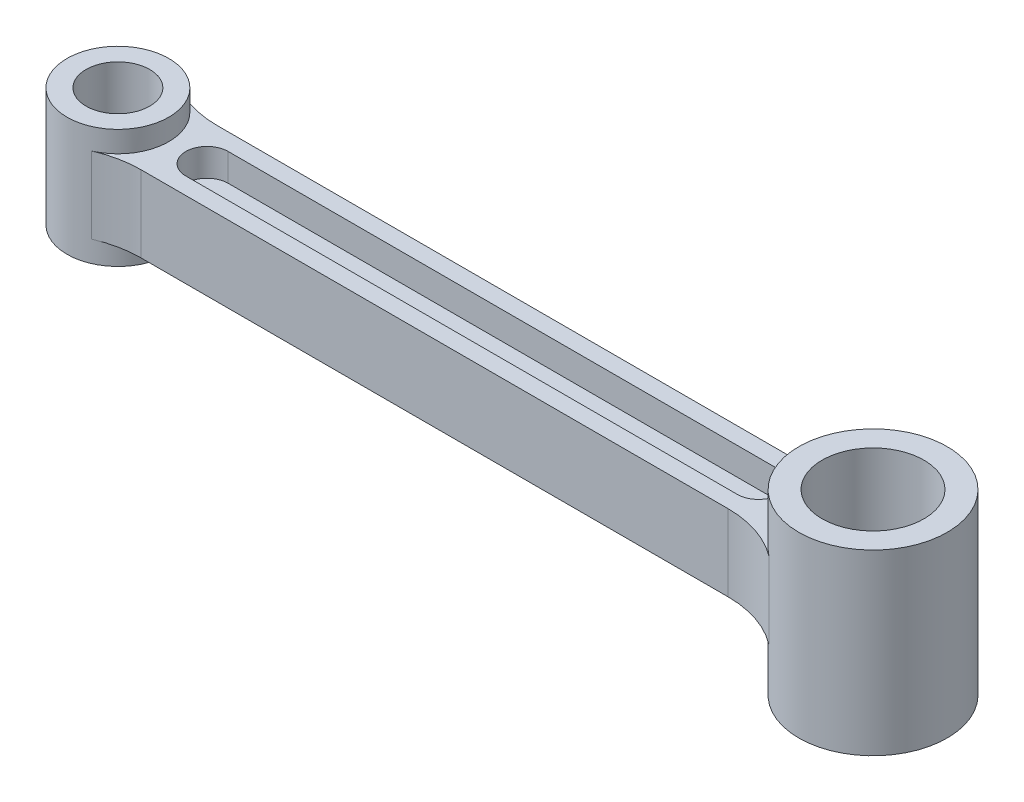
SolidWorks part; units mm, degrees
ref_plane "Front Plane" through (0, 0, 0) normal (0, 0, 1) x (1, 0, 0)
ref_plane "Top Plane" through (0, 0, 0) normal (0, 1, 0) x (1, 0, 0)
ref_plane "Right Plane" through (0, 0, 0) normal (1, 0, 0) x (0, 0, -1)
sketch "Sketch1" plane through (0, 0, 0) normal (0, 1, 0) x (1, 0, 0)
  circle A0 centre (0, 0) radius 7.5
  circle A1 centre (0, 0) radius 12
  dimension "D1" = 24
  dimension "D2" = 15
extrude "Boss-Extrude1" add sketch "Sketch1" along normal mid plane 28
sketch "Sketch3" plane through (0, 0, 0) normal (0, 1, 0) x (1, 0, 0)
  circle A0 centre (178, 0) radius 12
  circle A1 centre (178, 0) radius 17.5
  dimension "D1" = 35
  dimension "D2" = 24
  dimension "D3" = 178
extrude "Boss-Extrude2" add sketch "Sketch3" along normal mid plane 42 separate body
sketch "Sketch4" plane through (0, 0, 0) normal (0, 1, 0) x (1, 0, 0)
  line L1 (7.9373, 9) -> (162.9917, 9)
  line L3 (7.9373, -9) -> (162.9917, -9)
  circle A0 centre (0, 0) radius 12 construction
  arc A1 (7.9373, -9) -> (7.9373, 9) centre (0, 0) ccw
  circle A2 centre (178, 0) radius 17.5 construction
  arc A3 (162.9917, 9) -> (162.9917, -9) centre (178, 0) ccw
  dimension "D1" = 18
  dimension "D2" = 9
extrude "Boss-Extrude3" add sketch "Sketch4" along normal mid plane 18
sketch "Sketch5" plane through (0, 9, 0) normal (0, 1, 0) x (1, 0, 0)
  line L1 (21, 5) -> (151, 5)
  line L3 (21, -5) -> (151, -5)
  arc A0 (21, 5) -> (21, -5) centre (21, 0) ccw
  arc A1 (151, 5) -> (151, -5) centre (151, 0) cw
  dimension "D1" = 21
  dimension "D2" = 130
  dimension "D3" = 10
  dimension "D4" = 5
extrude "Cut-Extrude1" cut sketch "Sketch5" against normal blind 6.5
mirror "Mirror1" about plane through (0, 0, 0) normal (0, 1, 0) of "Cut-Extrude1"
fillet "Fillet1" radius 24 4 edges at (7.9373, 0, -9) (162.9917, 0, -9) (162.9917, 0, 9) (7.9373, 0, 9)
